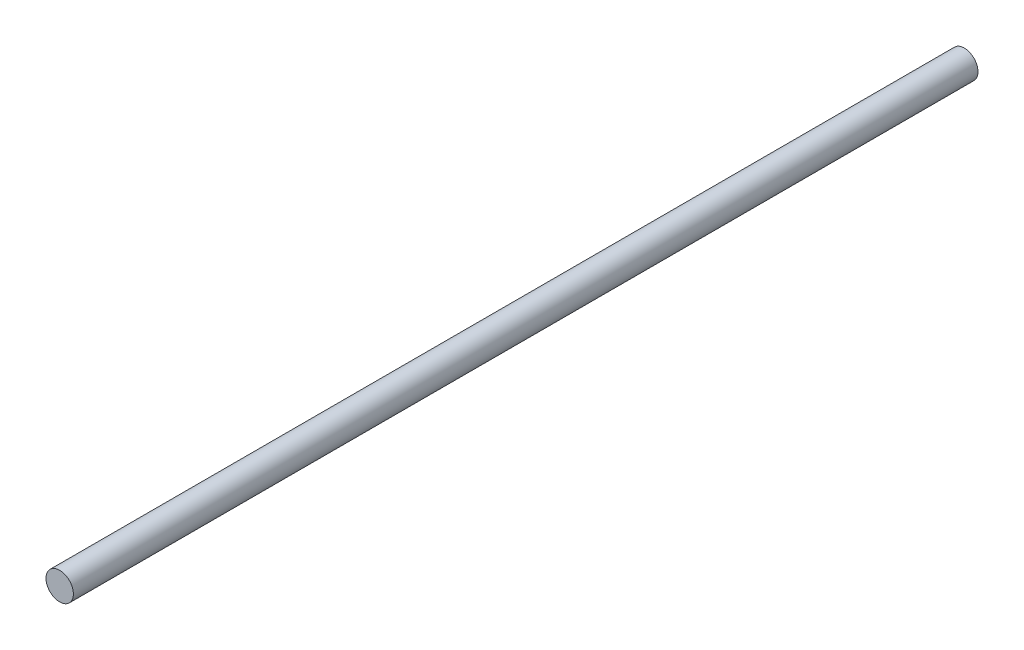
SolidWorks part; units mm, degrees
ref_plane "Front Plane" through (0, 0, 0) normal (0, 0, 1) x (1, 0, 0)
ref_plane "Top Plane" through (0, 0, 0) normal (0, 1, 0) x (1, 0, 0)
ref_plane "Right Plane" through (0, 0, 0) normal (1, 0, 0) x (0, 0, -1)
sketch "Sketch1" plane through (0, 0, 0) normal (0, 0, 1) x (1, 0, 0)
  circle A0 centre (0, 0) radius 2.5
  dimension "D1" = 5
extrude "Boss-Extrude1" add sketch "Sketch1" along normal blind 165
